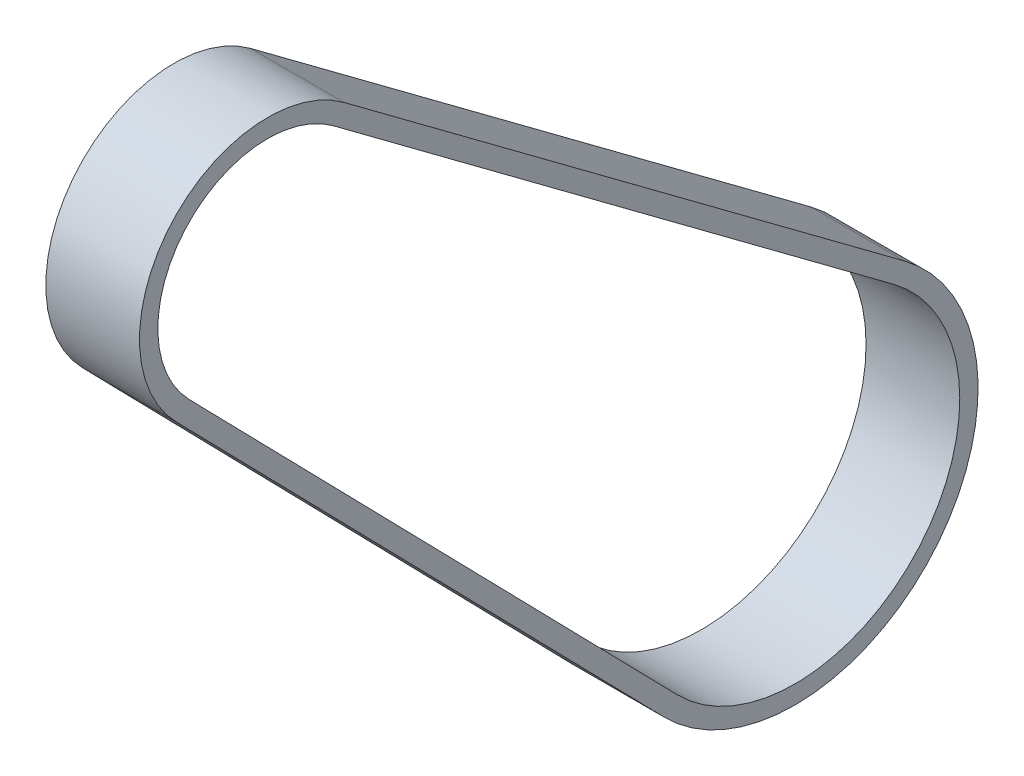
SolidWorks part; units mm, degrees
material "Default"
ref_plane "Top" through (0, 0, 0) normal (0, 0, 1) x (1, 0, 0)
ref_plane "Right" through (0, 0, 0) normal (0, 1, 0) x (1, 0, 0)
ref_plane "Front" through (0, 0, 0) normal (1, 0, 0) x (0, 0, -1)
ref_plane "Plane1" through (-63.1347, 0, 0) normal (1, 0, 0) x (0, 0, -1)
sketch "Sketch1" plane through (-63.1347, 0, 0) normal (1, 0, 0) x (0, 0, -1)
  line L0 (-54.7274, -67.414) -> (-18.1528, -99.414) construction
  line L1 (-60.1792, -72.7379) -> (-26.3304, -107.3998)
  line L2 (-50.1749, -61.3035) -> (-11.324, -90.2482)
  line L3 (-61.0878, -73.6252) -> (-27.239, -108.2871)
  line L4 (-49.4162, -60.285) -> (-10.5653, -89.2297)
  arc A0 (-50.1749, -61.3035) -> (-60.1792, -72.7379) centre (-54.7274, -67.414) ccw
  arc A1 (-26.3304, -107.3998) -> (-11.324, -90.2482) centre (-18.1528, -99.414) ccw
  arc A2 (-46.5029, -64.0392) -> (-61.0878, -73.6252) centre (-54.7274, -67.414) ccw
  arc A3 (-27.239, -108.2871) -> (-10.5653, -89.2297) centre (-18.1528, -99.414) ccw
  dimension "D1" = 15.24
  dimension "D2" = 22.86
  dimension "D3" = 1.27
  dimension "D4" = 1.27
extrude "Boss-Extrude1" add sketch "Sketch1" along normal up to surface (6.5 mm away)
